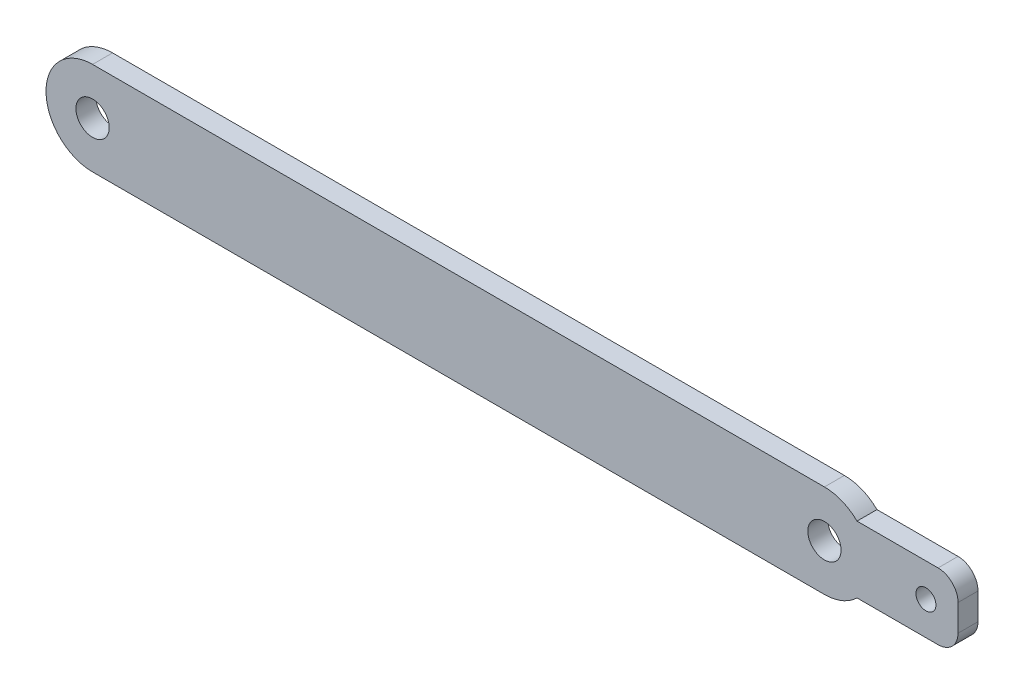
SolidWorks part; units mm, degrees
ref_plane "前视基准面" through (0, 0, 0) normal (0, 0, 1) x (1, 0, 0)
ref_plane "上视基准面" through (0, 0, 0) normal (0, 1, 0) x (1, 0, 0)
ref_plane "右视基准面" through (0, 0, 0) normal (1, 0, 0) x (0, 0, -1)
sketch "Sketch1" plane through (0, 0, 0) normal (0, 0, 1) x (1, 0, 0)
  line L0 (-70.959, 262.1541) -> (39.041, 262.1541) construction
  line L1 (-70.959, 269.1541) -> (39.041, 269.1541)
  line L2 (39.041, 255.1541) -> (-70.959, 255.1541)
  circle A0 centre (-70.959, 262.1541) radius 2.5
  circle A1 centre (39.041, 262.1541) radius 2.5
  circle A2 centre (-70.959, 262.1541) radius 7 construction
  circle A3 centre (39.041, 262.1541) radius 7 construction
  arc A4 (-70.959, 269.1541) -> (-70.959, 255.1541) centre (-70.959, 262.1541) ccw
  arc A5 (39.041, 255.1541) -> (39.041, 269.1541) centre (39.041, 262.1541) ccw
  dimension "D1" = 110
  dimension "D2" = 5
  dimension "D3" = 5
extrude "Boss-Extrude1" add sketch "Sketch1" along normal blind 3
sketch "Sketch2" plane through (0, 0, 3) normal (0, 0, 1) x (1, 0, 0)
  line L0 (41.041, 262.1541) -> (47.0645, 262.1541) construction
  line L1 (51.0678, 262.1541) -> (51.0678, 268.4295) construction
  line L2 (56.1254, 267.1541) -> (42.5811, 267.1541)
  line L3 (59.1254, 264.1541) -> (59.1254, 260.1541)
  line L4 (56.1254, 257.1541) -> (42.5811, 257.1541)
  line L5 (42.5811, 267.1541) -> (42.5811, 257.1541)
  line L6 (59.1254, 267.1541) -> (42.5811, 257.1541) construction
  line L7 (59.1254, 257.1541) -> (42.5811, 267.1541) construction
  arc A1 (59.1254, 260.1541) -> (56.1254, 257.1541) centre (56.1254, 260.1541) cw
  arc A2 (56.1254, 267.1541) -> (59.1254, 264.1541) centre (56.1254, 264.1541) cw
  circle A5 centre (54.3037, 262.1541) radius 1.5
  point P1 (50.8532, 262.1541)
  point P14 (54.3037, 262.1541)
  point P18 (63.1298, 262.1541)
  point P21 (54.7429, 262.1541)
  point P22 (61.1564, 262.1541)
  dimension "D1" = 3
  dimension "D3" = 10
extrude "Boss-Extrude2" add sketch "Sketch2" against normal up to surface (3 mm away) up to face at (-15.959, 262.1541, 0)
